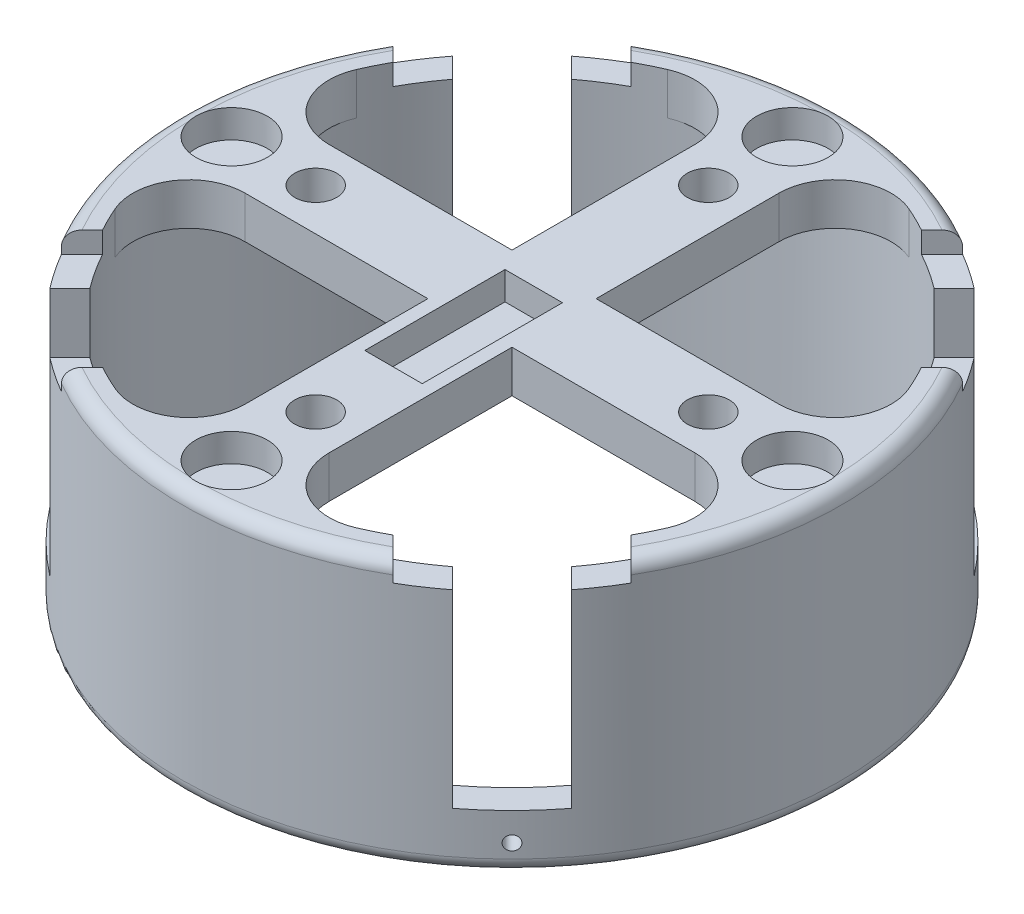
SolidWorks part; units mm, degrees
material "ABS"
ref_plane "Front Plane" through (0, 0, 0) normal (0, 0, 1) x (1, 0, 0)
ref_plane "Top Plane" through (0, 0, 0) normal (0, 1, 0) x (1, 0, 0)
ref_plane "Right Plane" through (0, 0, 0) normal (1, 0, 0) x (0, 0, -1)
sketch "Sketch5" plane through (0, 0, 0) normal (0, 1, 0) x (1, 0, 0)
  circle A0 centre (0, 0) radius 21.5
  circle A1 centre (0, 0) radius 23.5
  dimension "D1" = 43
  dimension "D2" = 47
extrude "Boss-Extrude3" add sketch "Sketch5" along normal blind 19
sketch "Sketch6" plane through (0, 19, 0) normal (0, 1, 0) x (1, 0, 0)
  line L0 (0, 14) -> (0, 0) construction
  line L1 (-3, 0) -> (-3, 21.2897)
  line L2 (3, 0) -> (3, 21.2897)
  line L3 (-3, 0) -> (3, 0)
  circle A0 centre (0, 14) radius 1.5
  circle A2 centre (0, 0) radius 21.5 construction
  arc A3 (3, 21.2897) -> (-3, 21.2897) centre (0, 0) ccw
  dimension "D2" = 3
  dimension "D3" = 3
  dimension "D1" = 14
  dimension "D4" = 3
extrude "Boss-Extrude4" add sketch "Sketch6" against normal blind 3
pattern_circular "CirPattern1" count 4 over 360 about axis through (0, 0, 0) along (0, 1, 0) of "Boss-Extrude4"
fillet "Fillet1" radius 4 8 edges at (-3, 17.5, -21.2897) (3, 17.5, -21.2897) (-21.2897, 17.5, -3) (-21.2897, 17.5, 3) (3, 17.5, 21.2897) (-3, 17.5, 21.2897) (21.2897, 17.5, -3) (21.2897, 17.5, 3)
sketch "Sketch7" plane through (0, 19, 0) normal (0, 1, 0) x (1, 0, 0)
  line L0 (0, 0) -> (16.617, 16.617) construction
  line L1 (16.039, 3) -> (3, 3) construction
  line L2 (21.3419, 17.0993) -> (16.1347, 11.8921)
  line L3 (21.3419, 17.0993) -> (17.0993, 21.3419)
  line L4 (16.1347, 11.8921) -> (11.8921, 16.1347)
  line L5 (17.0993, 21.3419) -> (11.8921, 16.1347)
  line L6 (21.3419, 17.0993) -> (11.8921, 16.1347) construction
  line L7 (16.1347, 11.8921) -> (17.0993, 21.3419) construction
  circle A0 centre (0, 0) radius 23.5 construction
  dimension "D1" = 45
  dimension "D2" = 6
extrude "Cut-Extrude1" cut sketch "Sketch7" against normal blind 15
pattern_circular "CirPattern2" count 4 over 360 about axis through (0, 0, 0) along (0, 1, 0) of "Cut-Extrude1"
sketch "Sketch8" plane through (0, 19, 0) normal (0, 1, 0) x (1, 0, 0)
  line L0 (-12.8598, 21.3451) -> (-7.3489, 15.8342)
  line L1 (-12.9327, 17.1754) -> (-14.3597, 18.6024) construction
  line L2 (-16.617, 16.617) -> (-15.2028, 15.2028) construction
  line L3 (-21.3451, 12.8598) -> (-15.8342, 7.3489)
  line L4 (-21.3451, 12.8598) -> (-12.8598, 21.3451)
  line L5 (-7.3489, 15.8342) -> (-15.8342, 7.3489)
  arc A0 (-14.3597, 18.6024) -> (-18.6024, 14.3597) centre (0, 0) ccw construction
  arc A1 (-12.9327, 17.1754) -> (-17.1754, 12.9327) centre (0, 0) ccw construction
  dimension "D1" = 3
extrude "Cut-Extrude2" cut sketch "Sketch8" against normal blind 1.5
pattern_circular "CirPattern3" count 4 over 360 about axis through (0, 0, 0) along (0, 1, 0) of "Cut-Extrude2"
fillet "Fillet2" radius 1 4 edges at (0, 19, -23.5) (23.5, 19, 0) (0, 19, 23.5) (-23.5, 19, 0)
fillet "Fillet3" radius 1 1 edges at (0, 0, 23.5)
ref_plane "Plane1" through (-16.481, 0, 16.481) normal (0.7071, 0, -0.7071) x (-0.7071, 0, -0.7071)
sketch "Sketch9" plane through (-16.481, 0, 16.481) normal (0.7071, 0, -0.7071) x (-0.7071, 0, -0.7071)
  line L0 (3, 4) -> (-3, 4) construction
  circle A0 centre (0, 2) radius 0.5
  dimension "D1" = 1
  dimension "D2" = 2
extrude "Cut-Extrude3" cut sketch "Sketch9" against normal up to next and the other way up to next
pattern_circular "CirPattern4" count 4 over 360 about axis through (0, 19, 0) along (0, -1, 0) of "Cut-Extrude3"
sketch "Sketch10" plane through (0, 19, 0) normal (0, 1, 0) x (1, 0, 0)
  circle A0 centre (0, 20) radius 2.55
  circle A1 centre (0, 14) radius 3 construction
  dimension "D1" = 5.1
  dimension "D2" = 20
extrude "Cut-Extrude4" cut sketch "Sketch10" against normal blind 2
pattern_circular "CirPattern5" count 4 over 360 about axis through (0, 0, 0) along (0, 1, 0) of "Cut-Extrude4"
sketch "Sketch11" plane through (0, 19, 0) normal (0, 1, 0) x (1, 0, 0)
  line L1 (2.05, -8.45) -> (-2.05, -8.45)
  line L2 (2.05, -8.45) -> (2.05, 1.55)
  line L3 (2.05, 1.55) -> (-2.05, 1.55)
  line L4 (-2.05, -8.45) -> (-2.05, 1.55)
  line L5 (2.05, -8.45) -> (-2.05, 1.55) construction
  line L6 (2.05, 1.55) -> (-2.05, -8.45) construction
  point P6 (0, 0)
  point P7 (0, 0)
  dimension "D1" = 4.1
  dimension "D2" = 10
  dimension "D3" = 1.55
  dimension "D4" = 2.05
extrude "Cut-Extrude5" cut sketch "Sketch11" against normal blind 2
